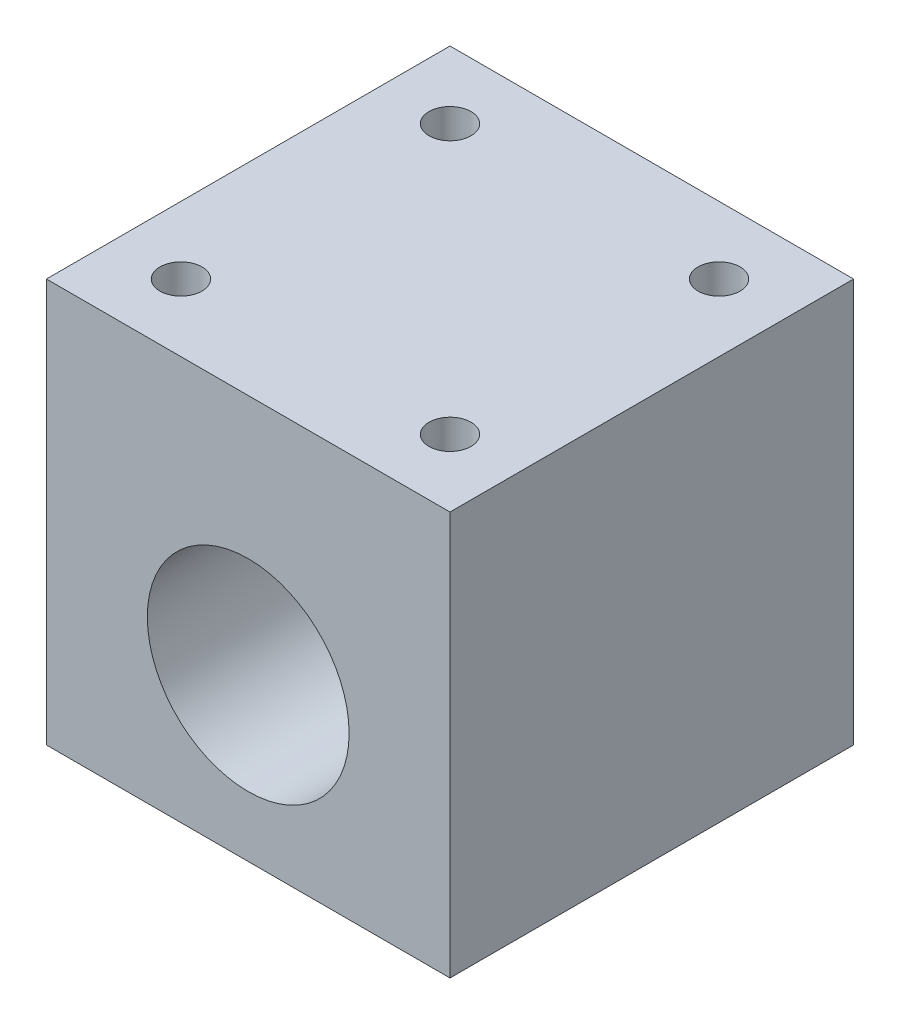
SolidWorks part; units mm, degrees
ref_plane "Front Plane" through (0, 0, 0) normal (0, 0, 1) x (1, 0, 0)
ref_plane "Top Plane" through (0, 0, 0) normal (0, 1, 0) x (1, 0, 0)
ref_plane "Right Plane" through (0, 0, 0) normal (1, 0, 0) x (0, 0, -1)
sketch "Sketch1" plane through (0, 0, 0) normal (0, 0, 1) x (1, 0, 0)
  line L1 (0, 0) -> (38.1, 0)
  line L2 (0, 0) -> (0, -38.1)
  line L3 (0, -38.1) -> (38.1, -38.1)
  line L4 (38.1, 0) -> (38.1, -38.1)
  dimension "D1" = 38.1
  dimension "3" = 38.1
extrude "Boss-Extrude1" add sketch "Sketch1" along normal blind 38.1
sketch "Sketch4" plane through (0, 0, 0) normal (0, 1, 0) x (1, 0, 0)
  line L0 (19.05, 0) -> (19.05, -50000) construction
  line L1 (38.1, 0) -> (0, 0) construction
  line L2 (38.1, -38.1) -> (0, -38.1) construction
  line L3 (0, -19.05) -> (50000, -19.05) construction
  line L4 (0, -38.1) -> (0, 0) construction
  line L5 (38.1, -38.1) -> (38.1, 0) construction
  circle A0 centre (6.35, -6.35) radius 1.9844
  circle A1 centre (6.35, -31.75) radius 1.9844
  circle A2 centre (31.75, -6.35) radius 1.9844
  circle A3 centre (31.75, -31.75) radius 1.9844
  point P4 (19.05, 0)
  point P7 (19.05, -38.1)
  point P12 (0, -19.05)
  point P15 (38.1, -19.05)
  dimension "D1" = 3.9688
  dimension "D2" = 12.7
  dimension "D3" = 12.7
extrude "Cut-Extrude2" cut sketch "Sketch4" against normal blind 19.05
hole_wizard "3/4 (0.75) Diameter Hole1" positions "Sketch8" profile "Sketch7" hole size "3/4" standard "ANSI Inch" end condition through all
sketch "Sketch8" plane through (0, 0, 38.1) normal (0, 0, 1) x (1, 0, 0)
  line L0 (0, 0) -> (0, -38.1) construction
  line L1 (0, -38.1) -> (38.1, -38.1) construction
  point P0 (19.05, -22.86)
  dimension "D1" = 19.05
  dimension "D2" = 15.24
sketch "Sketch7" plane through (19.05, -22.86, 38.1) normal (1, 0, 0) x (0, -1, 0)
  line L0 (0, 0) -> (0, 38.1)
  line L1 (0, 38.1) -> (9.525, 38.1)
  line L2 (9.525, 38.1) -> (9.525, 0)
  line L5 (9.525, 0) -> (0, 0)
  line L11 (0, -6.35) -> (0, 107.95) construction
  dimension "Thru Hole Dia." = 19.05
  dimension "Thru Hole Depth" = 38.1
